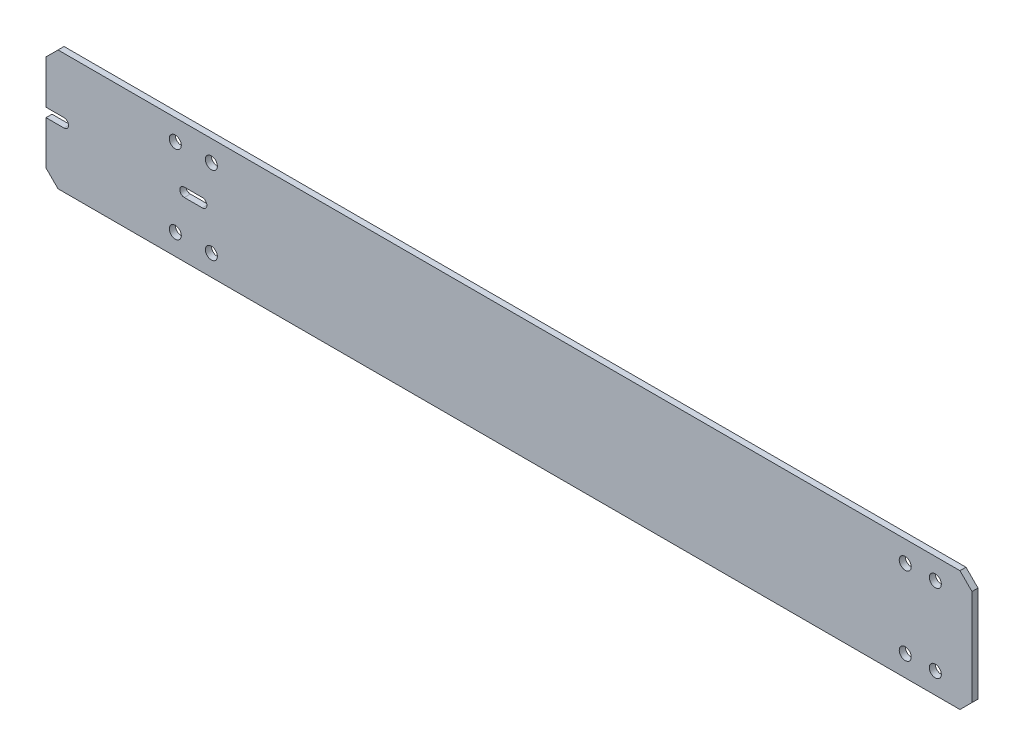
SolidWorks part; units mm, degrees
ref_plane "前视基准面" through (0, 0, 0) normal (0, 0, 1) x (1, 0, 0)
ref_plane "上视基准面" through (0, 0, 0) normal (0, 1, 0) x (1, 0, 0)
ref_plane "右视基准面" through (0, 0, 0) normal (1, 0, 0) x (0, 0, -1)
sketch "草图1" plane through (0, 0, 0) normal (0, 0, 1) x (1, 0, 0)
  line L1 (77, -10) -> (-77, -10)
  line L2 (77, -10) -> (77, 10)
  line L3 (77, 10) -> (-77, 10)
  line L4 (-77, -10) -> (-77, 10)
  line L5 (77, -10) -> (-77, 10) construction
  line L6 (77, 10) -> (-77, -10) construction
  point P0 (0, 0)
  dimension "D1" = 20
  dimension "D2" = 154
extrude "凸台-拉伸1" add sketch "草图1" along normal mid plane 1
chamfer "倒角1" distance 2 angle 45 4 edges at (77, -10, 0) (77, 10, 0) (-77, -10, 0) (-77, 10, 0)
sketch "草图2" plane through (0, 0, -0.5) normal (0, 0, -1) x (-1, 0, 0)
  line L0 (-67.4, 10) -> (-67.4, -10) construction
  line L1 (-67.4, -10) -> (-69.4, -10) construction
  line L2 (-69.4, -10) -> (-69.4, 10) construction
  line L3 (-69.4, 10) -> (-67.4, 10) construction
  line L5 (-75, 10) -> (75, 10) construction
  line L6 (75, -10) -> (-75, -10) construction
  line L7 (-69.4, 0) -> (-67.4, 0) construction
  line L8 (-77, -8) -> (-77, 8) construction
  circle A1 centre (-70.9, -6.5) radius 1
  circle A3 centre (-65.9, -6.5) radius 1
  circle A4 centre (-65.9, 6.5) radius 1
  circle A5 centre (-70.9, 6.5) radius 1
  point P10 (0, 0)
  point P11 (65.9, -5)
  dimension "D3" = 2
  dimension "D4" = 13
  dimension "D5" = 1.5
  dimension "D6" = 1.5
  dimension "D1" = 7.6
  dimension "D2" = 2
extrude "切除-拉伸1" cut sketch "草图2" against normal through all
sketch "草图3" plane through (0, 0, -0.5) normal (0, 0, -1) x (-1, 0, 0)
  line L0 (-75, 10) -> (75, 10) construction
  line L1 (51, 10) -> (54, 10) construction
  line L2 (51, 10) -> (51, -10) construction
  line L3 (51, -10) -> (54, -10) construction
  line L4 (54, 10) -> (54, -10) construction
  line L5 (75, -10) -> (-75, -10) construction
  line L6 (77, 8) -> (77, -8) construction
  line L7 (51, 0) -> (54, 0) construction
  circle A0 centre (55.5, 6.5) radius 1
  circle A1 centre (49.5, 6.5) radius 1
  circle A2 centre (55.5, -6.5) radius 1
  circle A3 centre (49.5, -6.5) radius 1
  dimension "D3" = 1.5
  dimension "D4" = 1.5
  dimension "D5" = 2
  dimension "D6" = 13
  dimension "D1" = 3
  dimension "D2" = 23
extrude "切除-拉伸2" cut sketch "草图3" against normal through all
sketch "草图4" plane through (0, 0, -0.5) normal (0, 0, -1) x (-1, 0, 0)
  line L1 (51, 0.75) -> (54, 0.75)
  line L2 (51, 0.75) -> (51, -0.75)
  line L3 (51, -0.75) -> (54, -0.75)
  line L4 (54, 0.75) -> (54, -0.75)
  line L5 (77, 8) -> (77, -8) construction
  line L6 (74, 0.75) -> (77, 0.75)
  line L7 (74, 0.75) -> (74, -0.75)
  line L8 (74, -0.75) -> (77, -0.75)
  line L9 (77, 0.75) -> (77, -0.75)
  point P4 (77, 0)
  dimension "D1" = 1.5
  dimension "D2" = 3
  dimension "D3" = 20
extrude "切除-拉伸3" cut sketch "草图4" against normal through all
sketch "草图5" plane through (0, 0, -0.5) normal (0, 0, -1) x (-1, 0, 0)
  line L0 (51, 0.75) -> (51, -0.75) construction
  line L1 (54, -0.75) -> (54, 0.75) construction
  line L2 (74, 0.75) -> (74, -0.75) construction
  circle A0 centre (51, 0) radius 0.75
  circle A1 centre (54, 0) radius 0.75
  circle A2 centre (74, 0) radius 0.75
extrude "切除-拉伸4" cut sketch "草图5" against normal through all
